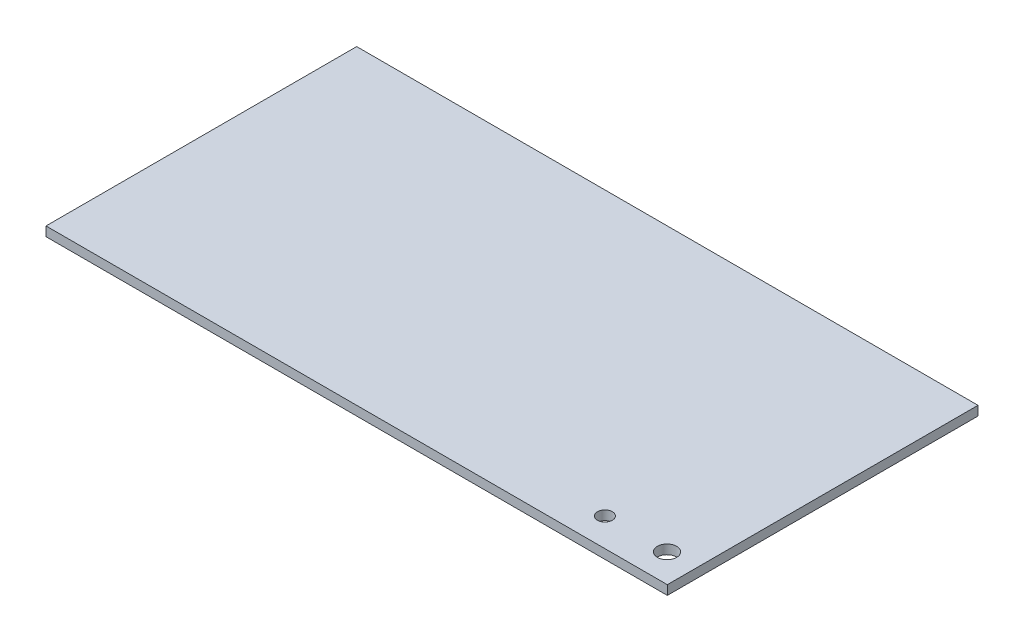
SolidWorks part; units mm, degrees
ref_plane "Front Plane" through (0, 0, 0) normal (0, 0, 1) x (1, 0, 0)
ref_plane "Top Plane" through (0, 0, 0) normal (0, 1, 0) x (1, 0, 0)
ref_plane "Right Plane" through (0, 0, 0) normal (1, 0, 0) x (0, 0, -1)
sketch "Sketch1" plane through (0, 0, 0) normal (0, 1, 0) x (1, 0, 0)
  line L1 (4460.2857, 2385.7143) -> (4714.2857, 2385.7143)
  line L2 (4460.2857, 2385.7143) -> (4460.2857, 2258.7143)
  line L3 (4460.2857, 2258.7143) -> (4714.2857, 2258.7143)
  line L4 (4714.2857, 2385.7143) -> (4714.2857, 2258.7143)
  dimension "D1" = 254
  dimension "D2" = 127
extrude "Boss-Extrude1" add sketch "Sketch1" along normal blind 3.81
sketch "Sketch2" plane through (0, 3.81, 0) normal (0, 1, 0) x (1, 0, 0)
  line L0 (4460.2857, 2270.2713) -> (4714.2857, 2270.2713) construction
  line L1 (4460.2857, 2385.7143) -> (4460.2857, 2258.7143) construction
  line L2 (4714.2857, 2258.7143) -> (4714.2857, 2385.7143) construction
  line L3 (4460.2857, 2258.7143) -> (4714.2857, 2258.7143) construction
  circle A0 centre (4677.2017, 2270.2713) radius 3.048
  circle A1 centre (4702.6017, 2270.2713) radius 3.937
  dimension "D1" = 7.874
  dimension "D2" = 6.096
  dimension "D3" = 11.557
  dimension "D4" = 11.684
  dimension "D5" = 25.4
extrude "Cut-Extrude1" cut sketch "Sketch2" against normal blind 25.4
